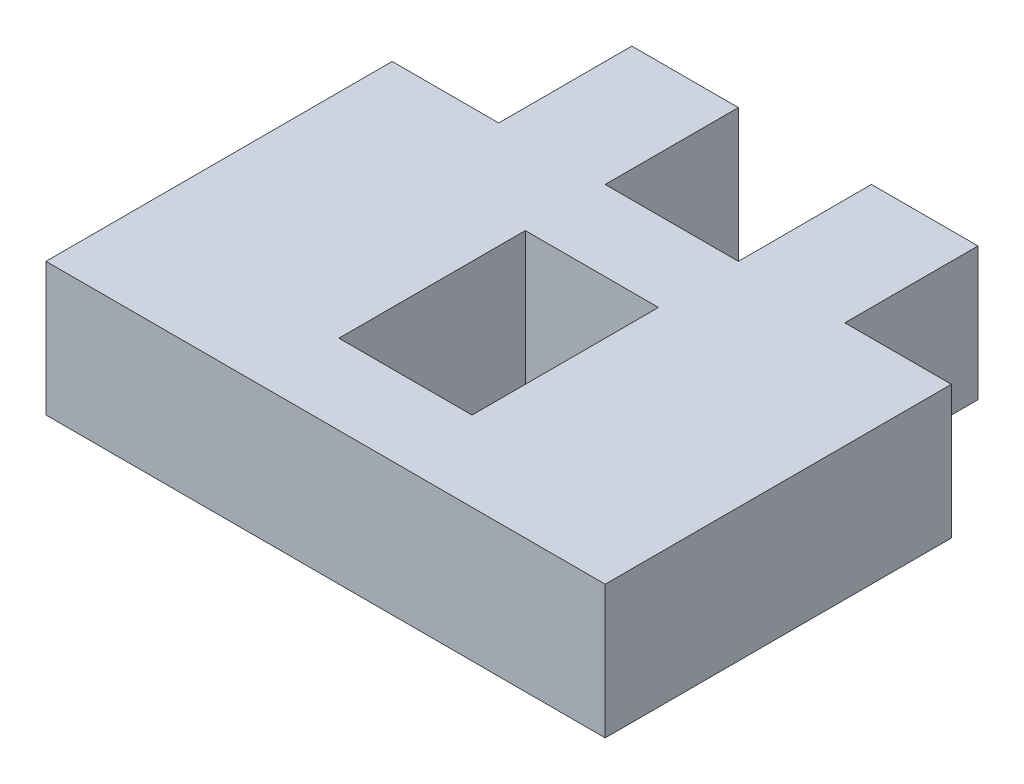
SolidWorks part; units mm, degrees
material "Balsa"
ref_plane "Alzado" through (0, 0, 0) normal (0, 0, 1) x (1, 0, 0)
ref_plane "Planta" through (0, 0, 0) normal (0, 1, 0) x (1, 0, 0)
ref_plane "Vista lateral" through (0, 0, 0) normal (1, 0, 0) x (0, 0, -1)
sketch "Croquis1" plane through (0, 0, 0) normal (0, 1, 0) x (1, 0, 0)
  line L1 (-14.0909, 11.9545) -> (6.9091, 11.9545)
  line L2 (-14.0909, 11.9545) -> (-14.0909, -6.0455)
  line L3 (-14.0909, -6.0455) -> (6.9091, -6.0455)
  line L4 (6.9091, 11.9545) -> (6.9091, -6.0455)
  line L17 (-6.0909, 11.9545) -> (-1.0909, 11.9545)
  line L18 (-6.0909, 11.9545) -> (-6.0909, 6.9545)
  line L19 (-6.0909, 6.9545) -> (-1.0909, 6.9545)
  line L20 (-1.0909, 11.9545) -> (-1.0909, 6.9545)
  line L21 (-14.0909, 6.9545) -> (-10.0909, 6.9545)
  line L22 (-14.0909, 6.9545) -> (-14.0909, 11.9545)
  line L23 (-14.0909, 11.9545) -> (-10.0909, 11.9545)
  line L24 (-10.0909, 6.9545) -> (-10.0909, 11.9545)
  line L29 (6.9091, 6.9545) -> (2.9091, 6.9545)
  line L30 (6.9091, 6.9545) -> (6.9091, 11.9545)
  line L31 (6.9091, 11.9545) -> (2.9091, 11.9545)
  line L32 (2.9091, 6.9545) -> (2.9091, 11.9545)
  dimension "D1" = 18
  dimension "D2" = 21
  dimension "D3" = 4
  dimension "D4" = 5
  dimension "D5" = 4
  dimension "D6" = 5
  dimension "D7" = 4
extrude "Saliente-Extruir1" add sketch "Croquis1" along normal blind 5
sketch "Croquis2" plane through (0, 5, 0) normal (0, 1, 0) x (1, 0, 0)
  line L0 (-14.0909, -6.0455) -> (6.9091, -6.0455) construction
  line L1 (-6.0909, 3.9545) -> (-1.0909, 3.9545)
  line L2 (-6.0909, 3.9545) -> (-6.0909, -3.0455)
  line L3 (-6.0909, -3.0455) -> (-1.0909, -3.0455)
  line L4 (-1.0909, 3.9545) -> (-1.0909, -3.0455)
  line L5 (-14.0909, 6.9545) -> (-14.0909, -6.0455) construction
  dimension "D1" = 7
  dimension "D2" = 5
  dimension "D3" = 3
  dimension "D4" = 8
extrude "Cortar-Extruir1" cut sketch "Croquis2" against normal blind 5
